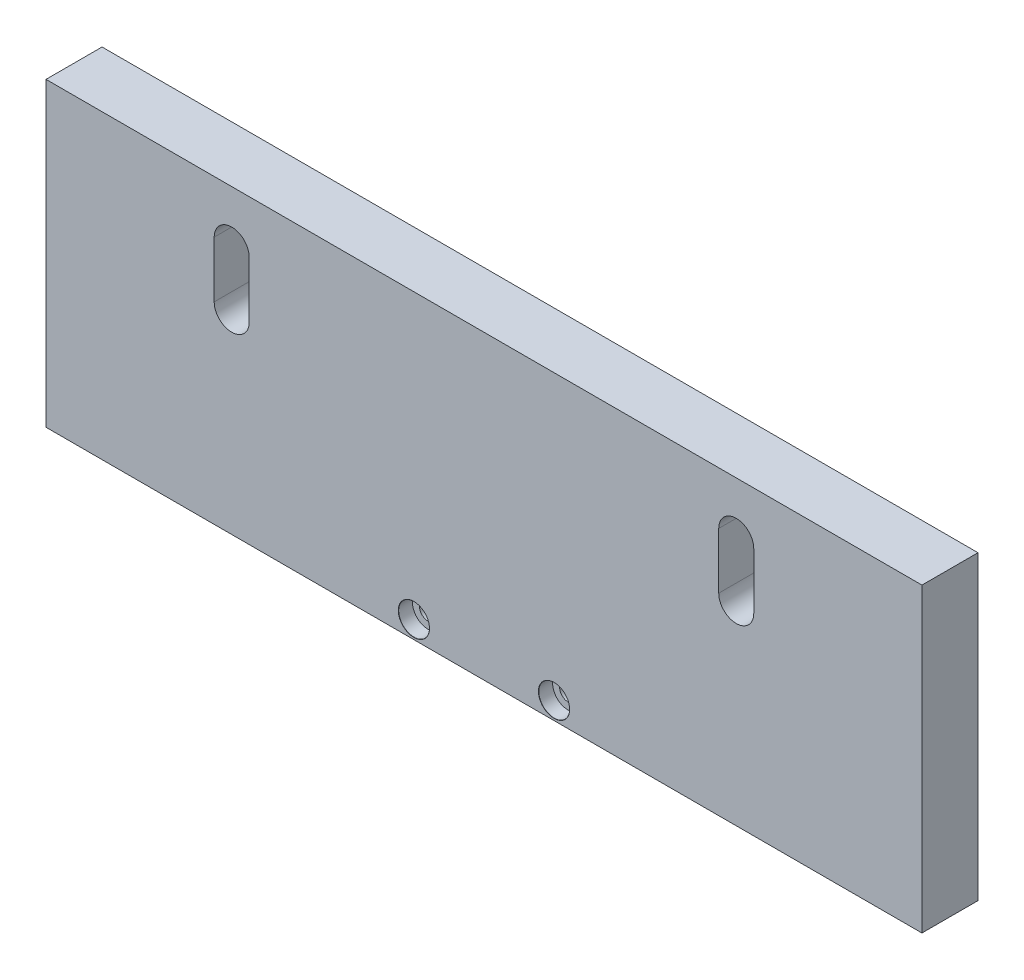
SolidWorks part; units mm, degrees
material "Liga 6061"
ref_plane "Plano frontal" through (0, 0, 0) normal (0, 0, 1) x (1, 0, 0)
ref_plane "Plano superior" through (0, 0, 0) normal (0, 1, 0) x (1, 0, 0)
ref_plane "Plano direito" through (0, 0, 0) normal (1, 0, 0) x (0, 0, -1)
sketch "Esboço1" plane through (0, 0, 0) normal (0, 0, 1) x (1, 0, 0)
  line L1 (62.5, -21.5) -> (-62.5, -21.5)
  line L2 (62.5, -21.5) -> (62.5, 21.5)
  line L3 (62.5, 21.5) -> (-62.5, 21.5)
  line L4 (-62.5, -21.5) -> (-62.5, 21.5)
  line L5 (62.5, -21.5) -> (-62.5, 21.5) construction
  line L6 (62.5, 21.5) -> (-62.5, -21.5) construction
  point P0 (0, 0)
  dimension "D1" = 43
  dimension "D2" = 125
extrude "Ressalto-extrusão1" add sketch "Esboço1" along normal blind 8
sketch "Esboço2" plane through (0, 0, 8) normal (0, 0, 1) x (1, 0, 0)
  line L0 (0, 24.6571) -> (0, -27.0388) construction
  line L1 (-66.5462, 0) -> (68.7877, 0) construction
  line L3 (-36, 28.0282) -> (-36, -28.8512) construction
  line L9 (62.5, 21.5) -> (-62.5, 21.5) construction
  line L12 (-33.5, 6) -> (-33.5, 14)
  line L16 (-38.5, 6) -> (-38.5, 14)
  line L17 (-33.5, 6) -> (-38.5, 14) construction
  line L18 (-33.5, 14) -> (-38.5, 6) construction
  line L19 (33.5, 14) -> (38.5, 6) construction
  line L20 (33.5, 6) -> (38.5, 14) construction
  line L21 (38.5, 6) -> (38.5, 14)
  line L22 (33.5, 6) -> (33.5, 14)
  arc A5 (-38.5, 6) -> (-33.5, 6) centre (-36, 6) ccw
  arc A6 (-33.5, 14) -> (-38.5, 14) centre (-36, 14) ccw
  arc A7 (33.5, 14) -> (38.5, 14) centre (36, 14) cw
  arc A8 (38.5, 6) -> (33.5, 6) centre (36, 6) cw
  point P11 (-36, 10)
  point P26 (36, 10)
  dimension "D3" = 36
  dimension "D4" = 8
  dimension "D5" = 5
  dimension "D6" = 11.5
extrude "Corte-extrusão1" cut sketch "Esboço2" against normal through all
hole_wizard "Rebaixo para SHCS M21" positions "Esboço3" profile "Esboço4" counterbore size "M2" standard "Ansi Metric" end condition through all
sketch "Esboço3" plane through (0, 0, 8) normal (0, 0, 1) x (1, 0, 0)
  line L0 (0, 24.0967) -> (0, -38.3866) construction
  line L2 (-62.5, -21.5) -> (62.5, -21.5) construction
  point P0 (-10, -19)
  point P2 (10, -19)
  dimension "D1" = 2.5
  dimension "D2" = 2.5
  dimension "D3" = 10
  dimension "D4" = 10
sketch "Esboço4" plane through (-10, -19, 8) normal (1, 0, 0) x (0, -1, 0)
  line L0 (0, 0) -> (0, 8)
  line L1 (0, 8) -> (1.2, 8)
  line L3 (1.2, 8) -> (1.2, 2)
  line L4 (2.2, 2) -> (1.2, 2)
  line L5 (2.2, 2) -> (2.2, 0.025)
  line L6 (2.2, 0.025) -> (2.225, 0)
  line L7 (2.225, 0) -> (0, 0)
  line L8 (-2.2, 0.025) -> (-2.225, 0) construction
  line L11 (0, -6.35) -> (0, 107.95) construction
  dimension "Thru Hole Dia." = 2.4
  dimension "Thru Hole Depth" = 8
  dimension "C'Bore Dia." = 4.4
  dimension "C'Bore Depth" = 2
  dimension "Near C'Sink Dia." = 4.45
  dimension "Near C'Sink Angle" = 90
sketch "Esboço6" plane through (0, 0, 0) normal (0, 0, -1) x (-1, 0, 0)
  line L0 (0, 25.3576) -> (0, -29.2803) construction
  line L1 (-67.9472, 0) -> (69.9085, 0) construction
  line L2 (62.5, -21.5) -> (-62.5, -21.5) construction
  circle A0 centre (0, 7) radius 11
  dimension "D1" = 22
  dimension "D2" = 28.5
extrude "Corte-extrusão2" cut sketch "Esboço6" against normal blind 7
